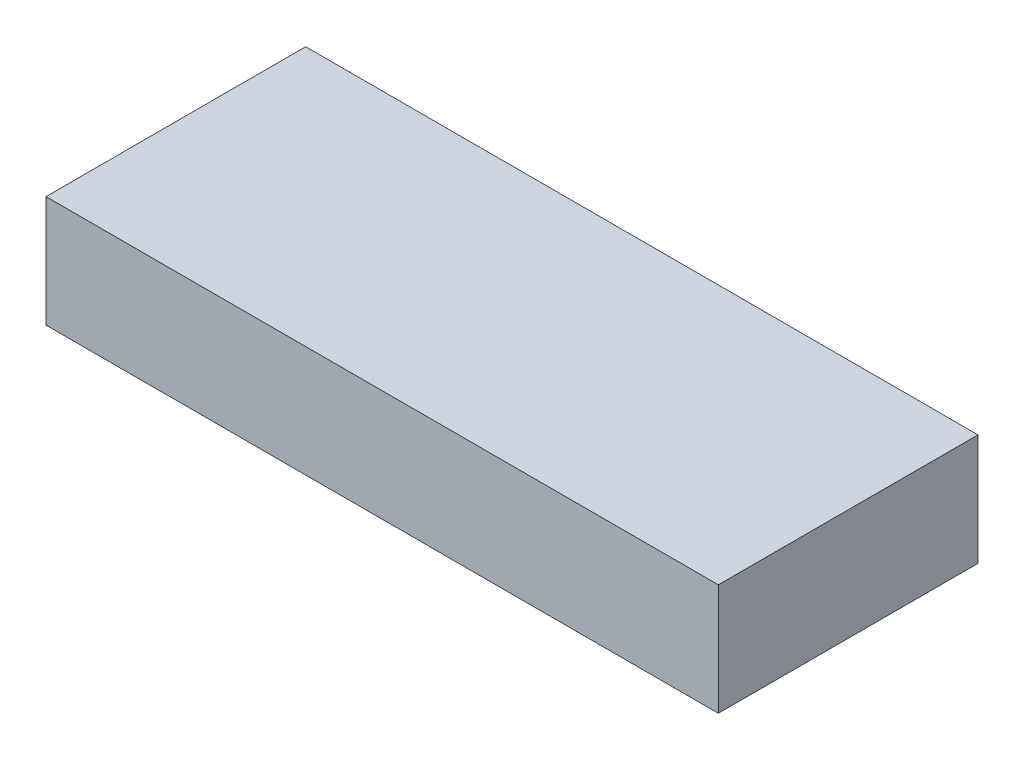
SolidWorks part; units mm, degrees
material "Pine"
ref_plane "Front Plane" through (0, 0, 0) normal (0, 0, 1) x (1, 0, 0)
ref_plane "Top Plane" through (0, 0, 0) normal (0, 1, 0) x (1, 0, 0)
ref_plane "Right Plane" through (0, 0, 0) normal (1, 0, 0) x (0, 0, -1)
sketch "Sketch1" plane through (0, 0, 0) normal (0, 1, 0) x (1, 0, 0)
  line L1 (0, 0) -> (230.1875, 0)
  line L2 (0, 0) -> (0, 88.9)
  line L3 (0, 88.9) -> (230.1875, 88.9)
  line L4 (230.1875, 0) -> (230.1875, 88.9)
  dimension "D1" = 88.9
  dimension "D2" = 230.1875
extrude "Boss-Extrude1" add sketch "Sketch1" along normal blind 38.1
